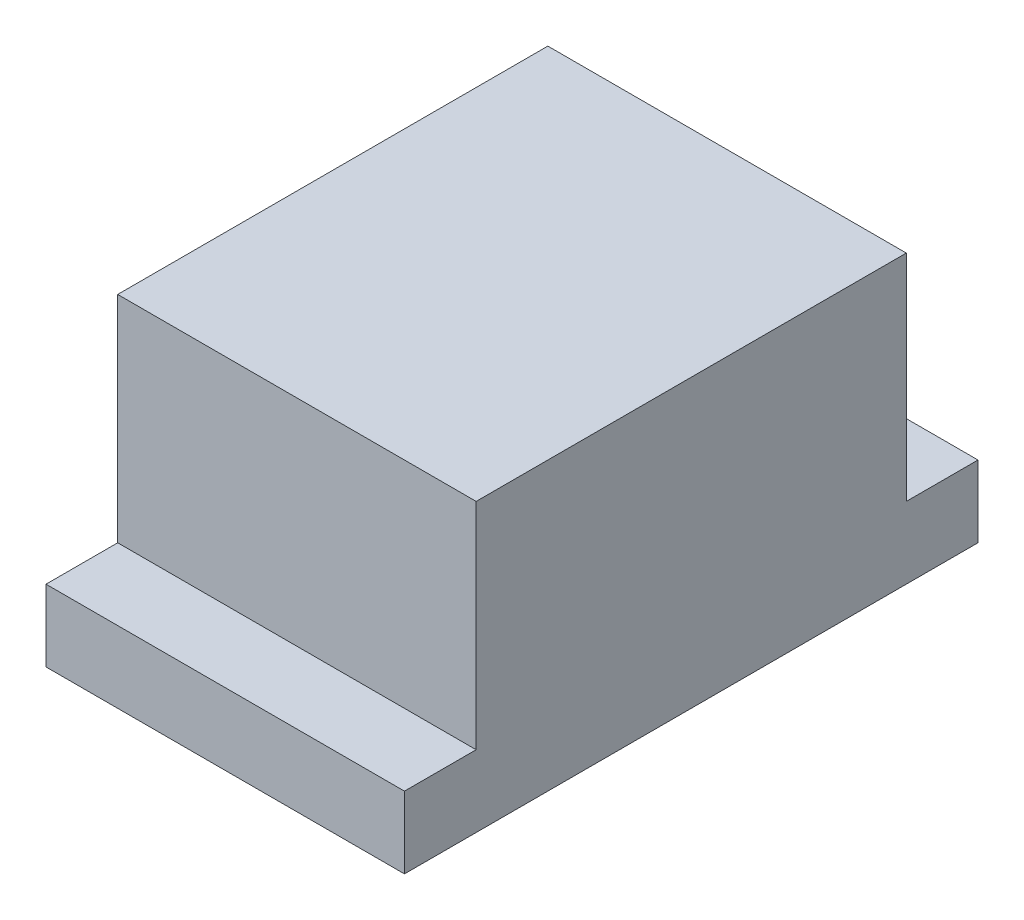
SolidWorks part; units mm, degrees
ref_plane "정면" through (0, 0, 0) normal (0, 0, 1) x (1, 0, 0)
ref_plane "윗면" through (0, 0, 0) normal (0, 1, 0) x (1, 0, 0)
ref_plane "우측면" through (0, 0, 0) normal (1, 0, 0) x (0, 0, -1)
sketch "스케치2" plane through (0, 0, 0) normal (1, 0, 0) x (0, 0, -1)
  line L0 (0, 0) -> (0, 40) construction
  line L1 (0, 0) -> (0, -38.1316) construction
  line L2 (-30, 40) -> (30, 40)
  line L3 (30, 40) -> (30, 10)
  line L4 (-30, 40) -> (-30, 10)
  line L5 (30, 10) -> (40, 10)
  line L6 (-30, 10) -> (-40, 10)
  line L7 (40, 10) -> (40, 0)
  line L8 (-40, 10) -> (-40, 0)
  line L9 (40, 0) -> (-40, 0)
  point P12 (0, 0)
  dimension "D1" = 60
  dimension "D2" = 10
  dimension "D3" = 40
  dimension "D4" = 80
extrude "보스-돌출1" add sketch "스케치2" along normal blind 50
